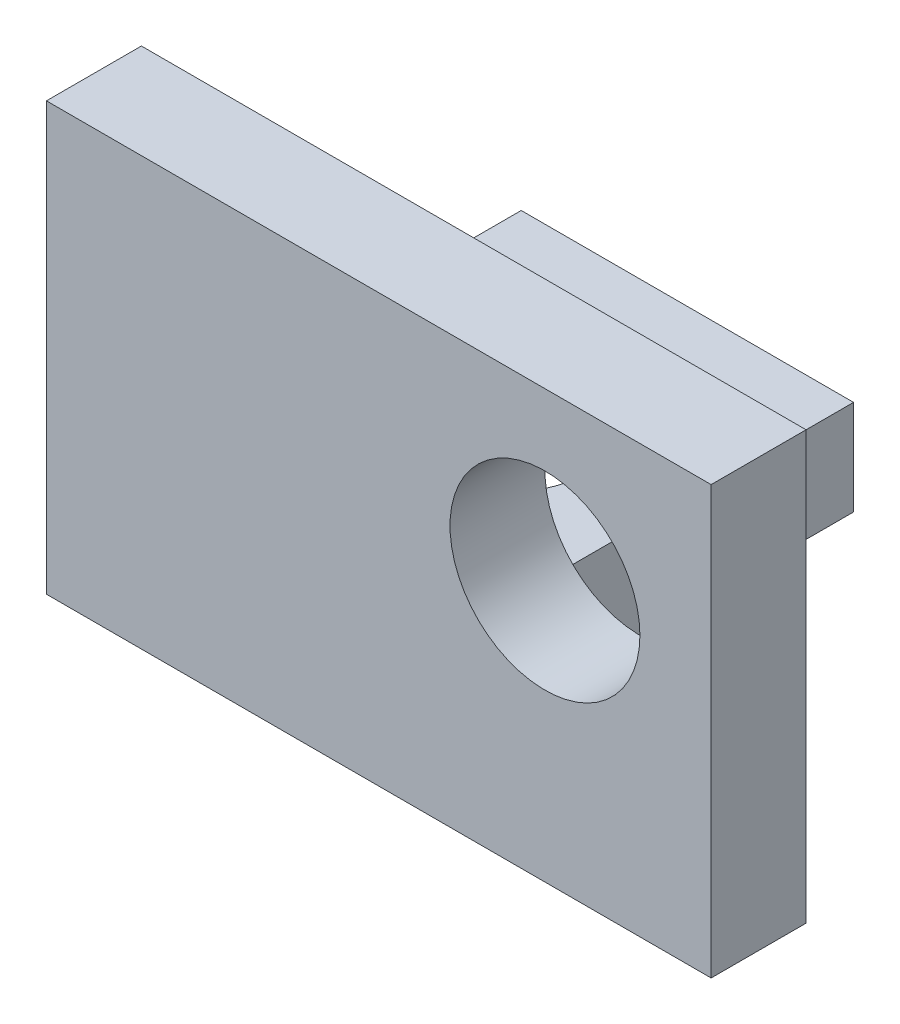
SolidWorks part; units mm, degrees
ref_plane "Front Plane" through (0, 0, 0) normal (0, 0, 1) x (1, 0, 0)
ref_plane "Top Plane" through (0, 0, 0) normal (0, 1, 0) x (1, 0, 0)
ref_plane "Right Plane" through (0, 0, 0) normal (1, 0, 0) x (0, 0, -1)
sketch "Sketch1" plane through (0, 0, 0) normal (0, 1, 0) x (1, 0, 0)
  line L0 (-4.445, 0) -> (-4.445, -5.08) construction
  line L1 (0, 0) -> (-8.89, 0)
  line L2 (0, 0) -> (0, -12.7)
  line L3 (0, -12.7) -> (-8.89, -12.7)
  line L4 (-8.89, 0) -> (-8.89, -12.7)
  line L5 (-4.445, -5.08) -> (-4.445, -12.7) construction
  circle A0 centre (-4.445, -5.08) radius 2.54
  dimension "D1" = 5.08
  dimension "D2" = 5.08
  dimension "D3" = 8.89
  dimension "D4" = 7.62
extrude "Boss-Extrude1" add sketch "Sketch1" along normal blind 2.54
sketch "Sketch2" plane through (0, 0, 12.7) normal (0, 0, 1) x (1, 0, 0)
  line L0 (4.445, 11.43) -> (4.445, 6.985) construction
  line L1 (-8.89, 0) -> (8.89, 0)
  line L2 (-8.89, 0) -> (-8.89, 11.43)
  line L3 (-8.89, 11.43) -> (8.89, 11.43)
  line L4 (8.89, 0) -> (8.89, 11.43)
  line L5 (4.445, 6.985) -> (8.89, 6.985) construction
  circle A0 centre (4.445, 6.985) radius 2.54
  dimension "D5" = 5.08
  dimension "D1" = 11.43
  dimension "D2" = 17.78
  dimension "D3" = 4.445
  dimension "D4" = 4.445
extrude "Boss-Extrude2" add sketch "Sketch2" against normal blind 2.54
equation "\"D3@Sketch2\"=(\"D1@Sketch2\"-.1)/2"
equation "\"D4@Sketch2\"=\"D3@Sketch2\""
